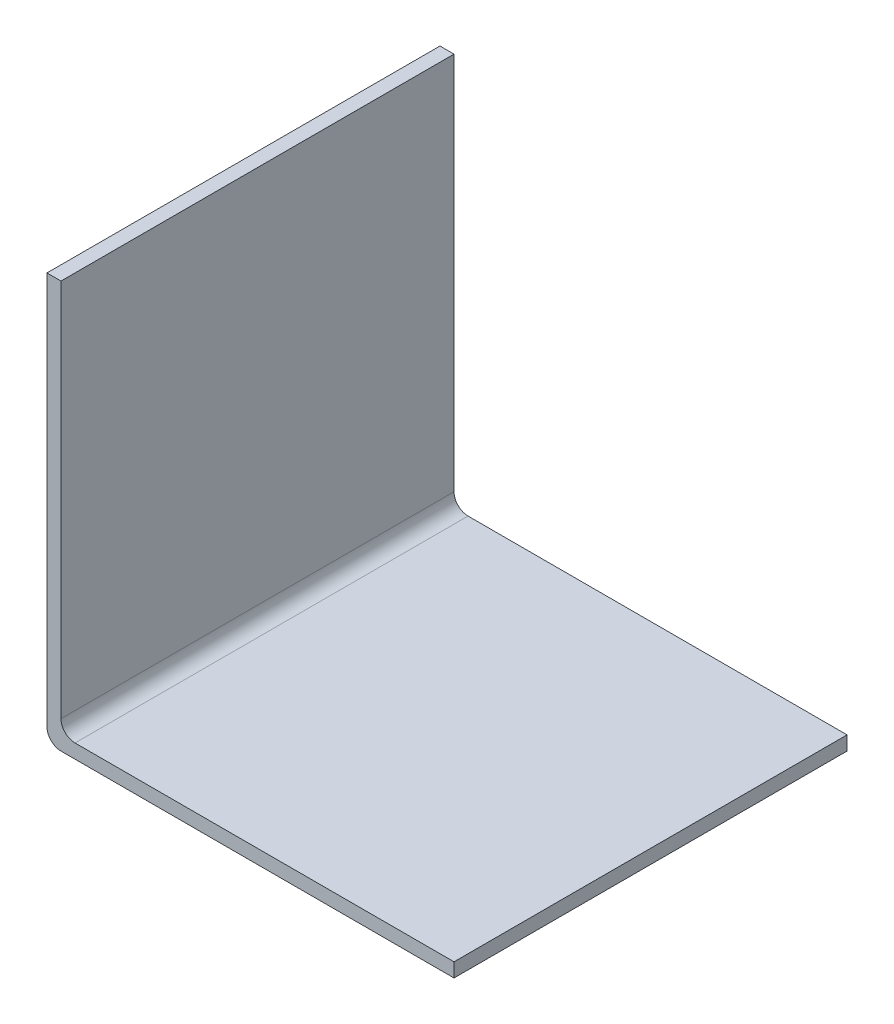
SolidWorks part; units mm, degrees
ref_plane "前视基准面" through (0, 0, 0) normal (0, 0, 1) x (1, 0, 0)
ref_plane "上视基准面" through (0, 0, 0) normal (0, 1, 0) x (1, 0, 0)
ref_plane "右视基准面" through (0, 0, 0) normal (1, 0, 0) x (0, 0, -1)
sketch "草图1" plane through (0, 0, 0) normal (0, 0, 1) x (1, 0, 0)
  line L0 (0, 28) -> (0, 0)
  line L1 (0, 0) -> (28, 0)
  dimension "D1" = 28
  dimension "D2" = 28
extrude "拉伸-薄壁1" add sketch "草图1" along normal blind 28 thin
fillet "圆角1" radius 1 2 edges at (-1, -1, 14) (0, 0, 14)
